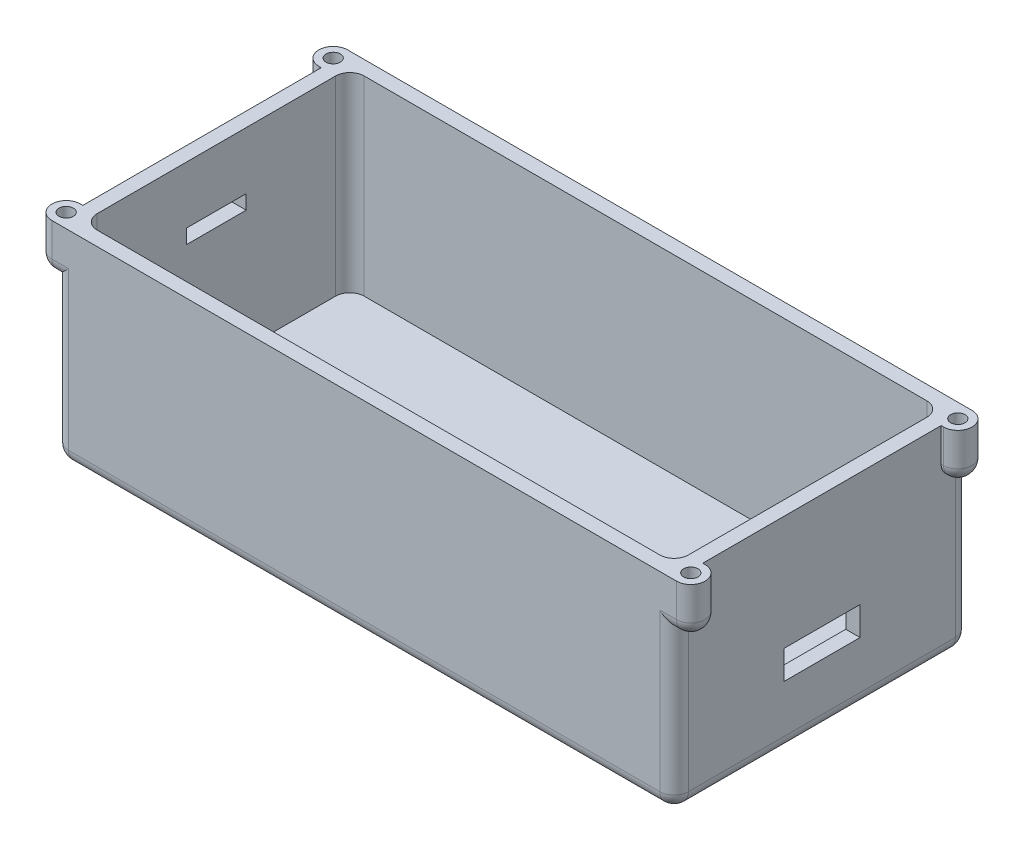
SolidWorks part; units mm, degrees
ref_plane "Front Plane" through (0, 0, 0) normal (0, 0, 1) x (1, 0, 0)
ref_plane "Top Plane" through (0, 0, 0) normal (0, 1, 0) x (1, 0, 0)
ref_plane "Right Plane" through (0, 0, 0) normal (1, 0, 0) x (0, 0, -1)
sketch "Sketch1" plane through (0, 0, 0) normal (0, 1, 0) x (1, 0, 0)
  line L1 (-65, -31) -> (65, -31)
  line L2 (-65, -31) -> (-65, 31)
  line L3 (-65, 31) -> (65, 31)
  line L4 (65, -31) -> (65, 31)
  line L5 (-65, -31) -> (65, 31) construction
  line L6 (-65, 31) -> (65, -31) construction
  point P0 (0, 0)
  dimension "D1" = 130
  dimension "D2" = 62
extrude "Boss-Extrude1" add sketch "Sketch1" along normal blind 3
sketch "Sketch2" plane through (0, 3, 0) normal (0, 1, 0) x (1, 0, 0)
  line L1 (62, -28) -> (-62, -28)
  line L2 (62, -28) -> (62, 28)
  line L3 (62, 28) -> (-62, 28)
  line L4 (-62, -28) -> (-62, 28)
  line L5 (62, -28) -> (-62, 28) construction
  line L6 (62, 28) -> (-62, -28) construction
  line L10 (65, -31) -> (65, 31)
  line L11 (65, 31) -> (-65, 31)
  line L12 (-65, 31) -> (-65, -31)
  line L13 (-65, -31) -> (65, -31)
  line L14 (65, -31) -> (65, 31)
  line L15 (65, 31) -> (-65, 31)
  line L16 (-65, 31) -> (-65, -31)
  line L17 (-65, -31) -> (65, -31)
  point P0 (0, 0)
  dimension "D2" = 3
  dimension "D3" = 3
  dimension "D1" = 0
extrude "Boss-Extrude2" add sketch "Sketch2" along normal blind 40
sketch "Sketch3" plane through (65, 0, 0) normal (1, 0, 0) x (0, 0, -1)
  line L0 (-31, 43) -> (31, 43) construction
  line L1 (-28, 43) -> (28, 43) construction
  line L2 (-28, 43) -> (-28, 3) construction
  line L3 (-28, 3) -> (28, 3) construction
  line L4 (28, 43) -> (28, 3) construction
  line L5 (-28, 43) -> (28, 3) construction
  line L6 (-28, 3) -> (28, 43) construction
  line L7 (-31, 0) -> (31, 0) construction
  line L8 (-31, 43) -> (-31, 0) construction
  line L10 (-8, 19) -> (8, 19)
  line L11 (-8, 19) -> (-8, 13)
  line L12 (-8, 13) -> (8, 13)
  line L13 (8, 19) -> (8, 13)
  line L14 (-8, 19) -> (8, 13) construction
  line L15 (-8, 13) -> (8, 19) construction
  point P4 (0, 23)
  point P7 (0, 0)
  point P17 (0, 16)
  dimension "D1" = 3
  dimension "D2" = 3
  dimension "D3" = 10
  dimension "D4" = 6
  dimension "D5" = 16
extrude "Cut-Extrude1" cut sketch "Sketch3" against normal up to next
sketch "Sketch4" plane through (-65, 0, 0) normal (-1, 0, 0) x (0, 0, 1)
  line L1 (-6.25, 31) -> (6.25, 31)
  line L2 (-6.25, 31) -> (-6.25, 28)
  line L3 (-6.25, 28) -> (6.25, 28)
  line L4 (-28, 3) -> (28, 3)
  line L5 (-28, 43) -> (-28, 3)
  line L6 (28, 43) -> (-28, 43)
  line L7 (28, 3) -> (28, 43)
  line L8 (-28, 3) -> (28, 3) construction
  line L9 (-28, 43) -> (-28, 3) construction
  line L10 (28, 43) -> (-28, 43) construction
  line L11 (28, 3) -> (28, 43) construction
  line L12 (6.25, 31) -> (6.25, 28)
  line L13 (-6.25, 31) -> (6.25, 28) construction
  line L14 (-6.25, 28) -> (6.25, 31) construction
  point P8 (0, 29.5)
  point P9 (0, 0)
  dimension "D2" = 25
  dimension "D3" = 3
  dimension "D4" = 12.5
  dimension "D1" = 0
extrude "Cut-Extrude2" cut sketch "Sketch4" against normal up to next
sketch "Sketch5" plane through (0, 43, 0) normal (0, 1, 0) x (1, 0, 0)
  line L0 (62, 28) -> (-62, 28) construction
  line L1 (65.5, -28) -> (-65.5, -28) construction
  line L2 (65.5, -28) -> (65.5, 28) construction
  line L3 (65.5, 28) -> (-65.5, 28) construction
  line L4 (-65.5, -28) -> (-65.5, 28) construction
  line L5 (65.5, -28) -> (-65.5, 28) construction
  line L6 (65.5, 28) -> (-65.5, -28) construction
  line L7 (-65, 31) -> (-65, -31) construction
  line L8 (-65, 31) -> (-65.5, 31)
  line L9 (-65, 31) -> (-65, 25)
  line L10 (-65, 25) -> (-65.5, 25)
  line L11 (-65.5, -25) -> (-65, -25)
  line L12 (-65, -25) -> (-65, -31)
  line L13 (-65, -31) -> (-65.5, -31)
  line L14 (65.5, 25) -> (65, 25)
  line L15 (65, -31) -> (65, 31) construction
  line L16 (65, 25) -> (65, 31)
  line L17 (65, 31) -> (65.5, 31)
  line L18 (65.5, -25) -> (65, -25)
  line L19 (65, -25) -> (65, -31)
  line L20 (65, -31) -> (65.5, -31)
  circle A1 centre (-65.5, 28) radius 1.5 construction
  circle A2 centre (-65.5, -28) radius 1.5 construction
  circle A3 centre (65.5, 28) radius 1.5 construction
  circle A4 centre (65.5, -28) radius 1.5 construction
  arc A5 (-65.5, 31) -> (-65.5, 25) centre (-65.5, 28) ccw
  arc A6 (-65.5, -31) -> (-65.5, -25) centre (-65.5, -28) cw
  arc A7 (65.5, 31) -> (65.5, 25) centre (65.5, 28) cw
  arc A8 (65.5, -31) -> (65.5, -25) centre (65.5, -28) ccw
  point P0 (0, 0)
  point P40 (0, 0)
  dimension "D1" = 3
  dimension "D2" = 0.5
extrude "Boss-Extrude3" add sketch "Sketch5" against normal blind 10
sketch "Sketch6" plane through (0, 43, 0) normal (0, 1, 0) x (1, 0, 0)
  circle A0 centre (-65.5, 28) radius 1.5 construction
  circle A1 centre (-65.5, 28) radius 1.5
  circle A2 centre (-65.5, -28) radius 1.5 construction
  circle A3 centre (-65.5, -28) radius 1.5
  circle A4 centre (65.5, -28) radius 1.5 construction
  circle A5 centre (65.5, -28) radius 1.5
  circle A6 centre (65.5, 28) radius 1.5 construction
  circle A7 centre (65.5, 28) radius 1.5
extrude "Cut-Extrude3" cut sketch "Sketch6" against normal blind 5
fillet "Fillet1" radius 3 8 edges at (-65, 16.5, 31) (-62, 23, 28) (62, 23, 28) (65, 16.5, 31) (65, 16.5, -31) (62, 23, -28) (-62, 23, -28) (-65, 16.5, -31)
fillet "Fillet2" radius 3 12 edges at (65.25, 33, -25) (63.75, 33, -31) (63.75, 33, 31) (65.25, 33, 25) (-63.75, 33, -31) (-65.25, 33, -25) (-65.25, 33, 25) (-63.75, 33, 31) (68.5, 33, -28) (68.5, 33, 28) (-68.5, 33, -28) (-68.5, 33, 28)
fillet "Fillet3" radius 3 8 edges at (-64.1213, 0, 30.1213) (-65, 0, 0) (-64.1213, 0, -30.1213) (0, 0, -31) (64.1213, 0, -30.1213) (65, 0, 0) (64.1213, 0, 30.1213) (0, 0, 31)
